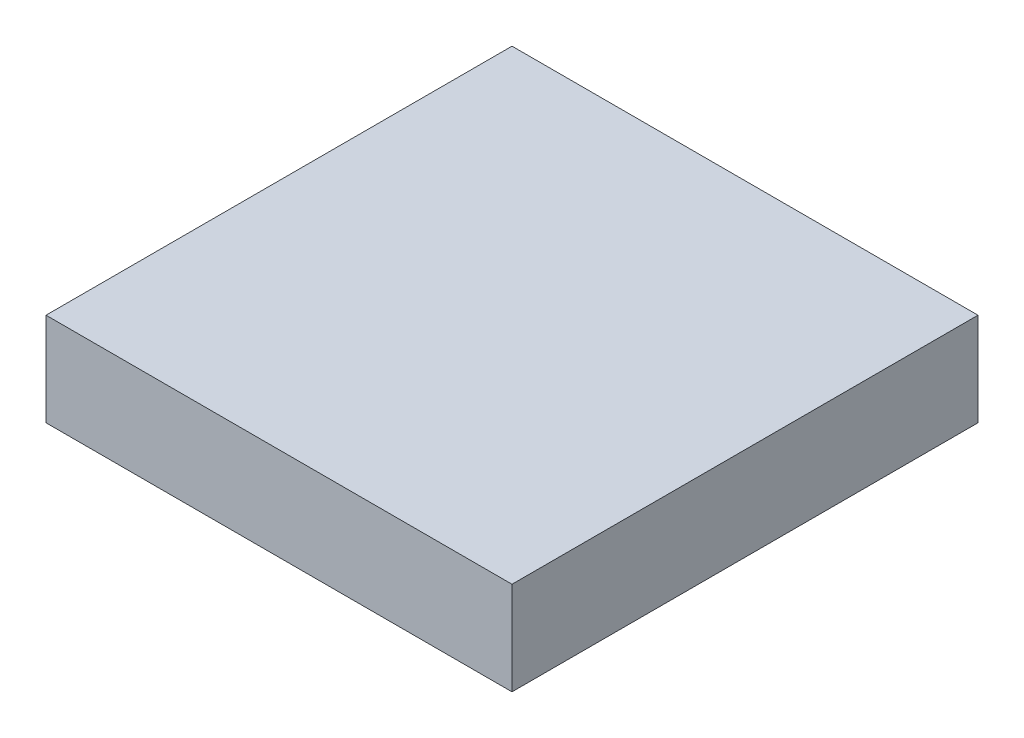
SolidWorks part; units mm, degrees
material "Water"
ref_plane "Front Plane" through (0, 0, 0) normal (0, 0, 1) x (1, 0, 0)
ref_plane "Top Plane" through (0, 0, 0) normal (0, 1, 0) x (1, 0, 0)
ref_plane "Right Plane" through (0, 0, 0) normal (1, 0, 0) x (0, 0, -1)
sketch "Sketch1" plane through (0, 0, 0) normal (0, 1, 0) x (1, 0, 0)
  line L1 (0, 0) -> (25400, 0)
  line L2 (0, 0) -> (0, 25400)
  line L3 (0, 25400) -> (25400, 25400)
  line L4 (25400, 0) -> (25400, 25400)
  dimension "D1" = 25400
  dimension "D2" = 25400
extrude "Boss-Extrude1" add sketch "Sketch1" along normal blind 5080
